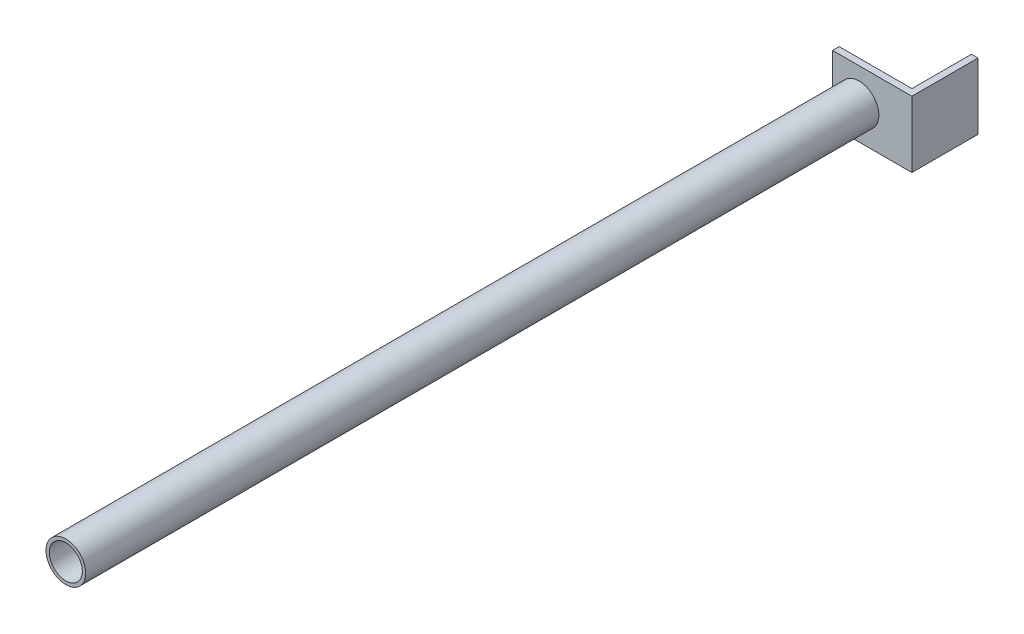
SolidWorks part; units mm, degrees
ref_plane "Front Plane" through (0, 0, 0) normal (0, 0, 1) x (1, 0, 0)
ref_plane "Top Plane" through (0, 0, 0) normal (0, 1, 0) x (1, 0, 0)
ref_plane "Right Plane" through (0, 0, 0) normal (1, 0, 0) x (0, 0, -1)
sketch "Sketch1" plane through (0, 0, 0) normal (0, 1, 0) x (1, 0, 0)
  line L0 (0, 31.75) -> (0, -31.75)
  line L1 (0, -34.925) -> (0, 34.925) construction
  line L2 (0, -31.75) -> (-76.2, -31.75)
  line L3 (-76.2, -31.75) -> (-76.2, -25.4)
  line L4 (-76.2, -25.4) -> (-6.35, -25.4)
  line L5 (-6.35, -25.4) -> (-6.35, 31.75)
  line L6 (-6.35, 31.75) -> (0, 31.75)
  dimension "D1" = 63.5
  dimension "D2" = 76.2
  dimension "D3" = 6.35
extrude "Boss-Extrude1" add sketch "Sketch1" along normal mid plane 63.5
sketch "Sketch2" plane through (0, 0, 31.75) normal (0, 0, 1) x (1, 0, 0)
  line L0 (-76.2, 31.75) -> (-76.2, -31.75) construction
  line L1 (55, 0) -> (-55, 0) construction
  circle A0 centre (-50.8, 0) radius 19.05
  circle A1 centre (-50.8, 0) radius 15.875
  dimension "D2" = 38.1
  dimension "D3" = 3.175
  dimension "D1" = 25.4
extrude "Boss-Extrude2" add sketch "Sketch2" along normal blind 762
sketch "Sketch3" [suppressed] plane through (0, 0, 31.75) normal (0, 0, 1) x (1, 0, 0)
  line L0 (55, 0) -> (-55, 0) construction
  line L1 (-12.7, 19.05) -> (-63.5, 19.05)
  line L2 (-12.7, 19.05) -> (-12.7, -19.05)
  line L3 (-12.7, -19.05) -> (-63.5, -19.05)
  line L4 (-63.5, 19.05) -> (-63.5, -19.05)
  line L5 (-12.7, 19.05) -> (-63.5, -19.05) construction
  line L6 (-12.7, -19.05) -> (-63.5, 19.05) construction
  line L7 (-76.2, 31.75) -> (-76.2, -31.75) construction
  point P0 (-38.1, 0)
  dimension "D1" = 38.1
  dimension "D2" = 50.8
  dimension "D3" = 38.1
extrude "Boss-Extrude3" [suppressed] add sketch "Sketch3" along normal blind 63.5
sketch "Sketch4" [suppressed] plane through (0, 0, 0) normal (0, 1, 0) x (1, 0, 0)
  line L0 (-38.1, -95.25) -> (-38.1, -298.45) construction
  line L1 (-12.7, -95.25) -> (-63.5, -95.25) construction
  line L2 (-12.7, -95.25) -> (-63.5, -95.25)
  line L3 (-57.15, -95.25) -> (-57.15, -120.65)
  line L4 (-57.15, -120.65) -> (-63.5, -146.05)
  line L5 (-63.5, -146.05) -> (-63.5, -171.45)
  line L6 (-63.5, -171.45) -> (-76.2, -285.75)
  line L7 (-76.2, -285.75) -> (-76.2, -298.45)
  line L8 (-76.2, -298.45) -> (-38.1, -298.45)
  dimension "D1" = 203.2
  dimension "D2" = 12.7
  dimension "D3" = 25.4
  dimension "D4" = 19.05
  dimension "D5" = 25.4
  dimension "D6" = 25.4
  dimension "D7" = 25.4
  dimension "D8" = 38.1
revolve "Revolve1" [suppressed] add sketch "Sketch4" angle 360 about L0
